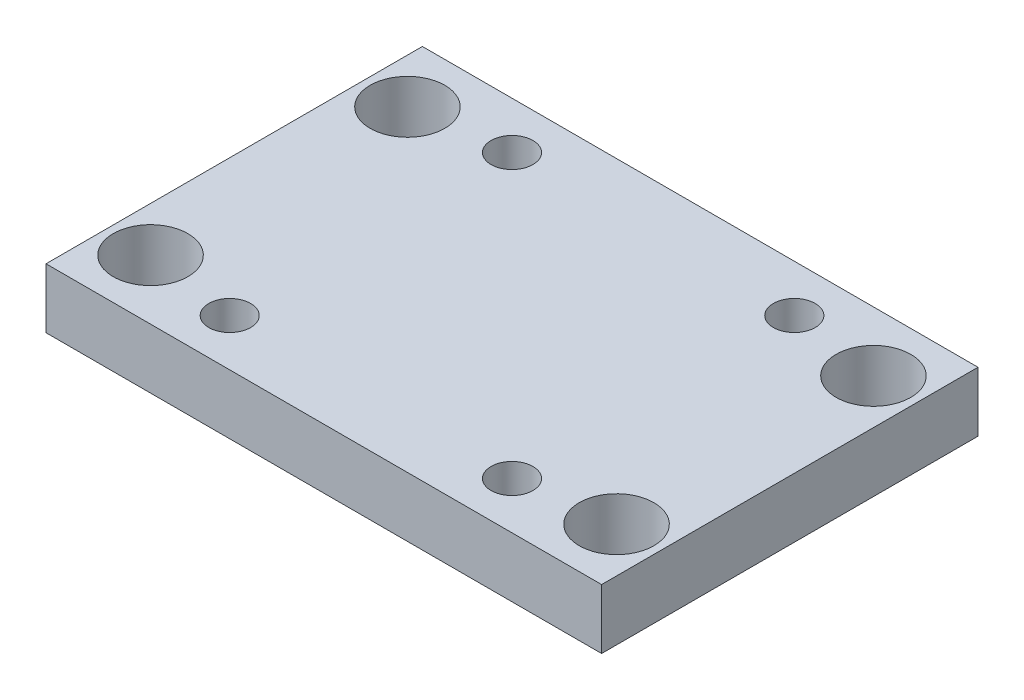
SolidWorks part; units mm, degrees
ref_plane "Front Plane" through (0, 0, 0) normal (0, 0, 1) x (1, 0, 0)
ref_plane "Top Plane" through (0, 0, 0) normal (0, 1, 0) x (1, 0, 0)
ref_plane "Right Plane" through (0, 0, 0) normal (1, 0, 0) x (0, 0, -1)
sketch "Sketch1" plane through (0, 0, 0) normal (0, 1, 0) x (1, 0, 0)
  line L1 (-59.055, 40.005) -> (59.055, 40.005)
  line L2 (-59.055, 40.005) -> (-59.055, -40.005)
  line L3 (-59.055, -40.005) -> (59.055, -40.005)
  line L4 (59.055, 40.005) -> (59.055, -40.005)
  line L5 (-59.055, 40.005) -> (59.055, -40.005) construction
  line L6 (-59.055, -40.005) -> (59.055, 40.005) construction
  point P0 (0, 0)
  dimension "D1" = 118.11
  dimension "D2" = 80.01
extrude "Boss-Extrude1" add sketch "Sketch1" along normal blind 12.7
sketch "Sketch2" plane through (0, 0, 0) normal (0, -1, 0) x (1, 0, 0)
  line L1 (-59.055, -40.005) -> (-59.055, 40.005) construction
  line L2 (59.055, 40.005) -> (59.055, -40.005) construction
  line L3 (-59.055, 40.005) -> (59.055, 40.005) construction
  line L4 (59.055, -40.005) -> (-59.055, -40.005) construction
  circle A0 centre (-30.005, 30.005) radius 4.445
  circle A1 centre (30.005, 30.005) radius 4.445
  circle A2 centre (-30.005, -30.005) radius 4.445
  circle A3 centre (30.005, -30.005) radius 4.445
  dimension "D1" = 8.89
  dimension "D2" = 8.89
  dimension "D3" = 8.89
  dimension "D4" = 8.89
  dimension "D5" = 29.05
  dimension "D6" = 29.05
  dimension "D7" = 29.05
  dimension "D8" = 29.05
  dimension "D9" = 10
  dimension "D10" = 10
  dimension "D11" = 10
  dimension "D12" = 10
extrude "Cut-Extrude1" cut sketch "Sketch2" against normal through all
sketch "Sketch3" plane through (0, 0, 0) normal (0, -1, 0) x (1, 0, 0)
  line L0 (-59.055, 40.005) -> (59.055, 40.005) construction
  line L1 (59.055, -40.005) -> (-59.055, -40.005) construction
  line L2 (59.055, 40.005) -> (59.055, -40.005) construction
  line L3 (-59.055, -40.005) -> (-59.055, 40.005) construction
  circle A0 centre (-49.53, 27.305) radius 7.9375
  circle A1 centre (-49.53, -27.305) radius 7.9375
  circle A2 centre (49.53, -27.305) radius 7.9375
  circle A3 centre (49.53, 27.305) radius 7.9375
  dimension "D1" = 15.875
  dimension "D2" = 15.875
  dimension "D3" = 15.875
  dimension "D4" = 15.875
  dimension "D5" = 12.7
  dimension "D6" = 12.7
  dimension "D7" = 12.7
  dimension "D8" = 12.7
  dimension "D9" = 9.525
  dimension "D10" = 9.525
  dimension "D11" = 9.525
  dimension "D12" = 9.525
extrude "Cut-Extrude2" cut sketch "Sketch3" against normal through all
